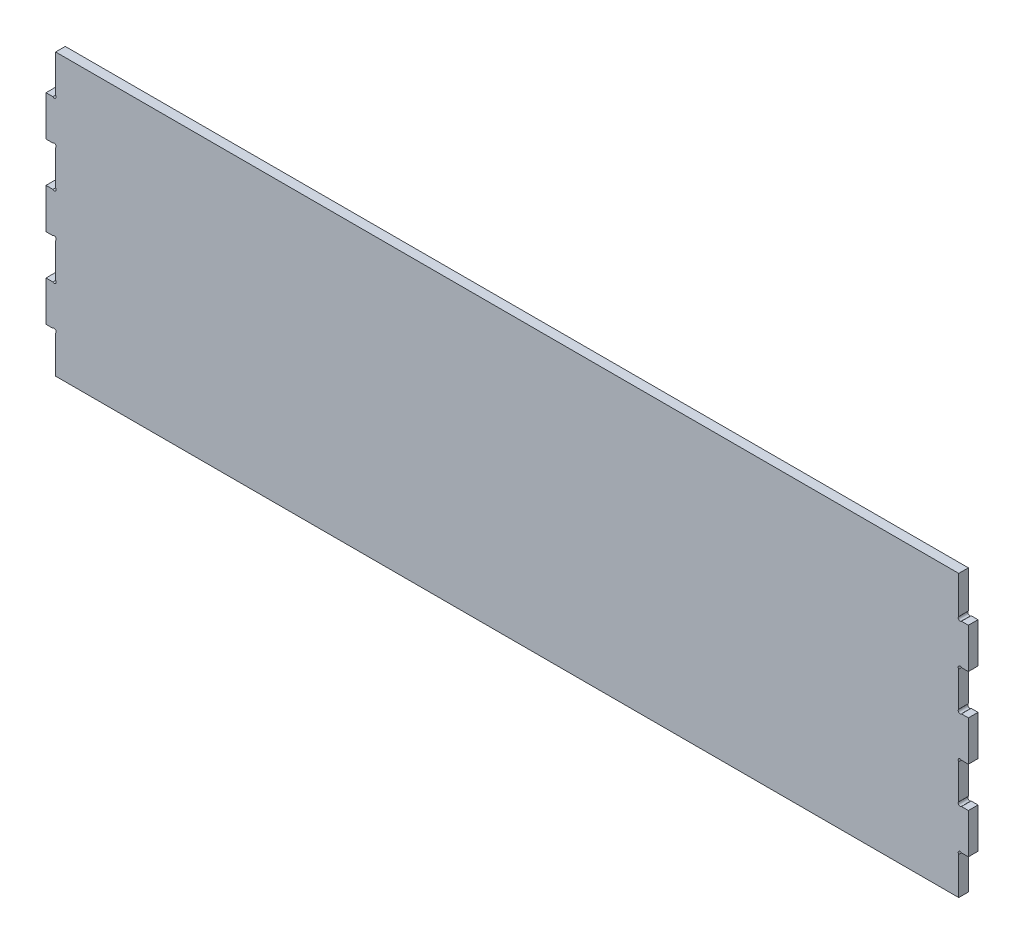
SolidWorks part; units mm, degrees
ref_plane "Front Plane" through (0, 0, 0) normal (0, 0, 1) x (1, 0, 0)
ref_plane "Top Plane" through (0, 0, 0) normal (0, 1, 0) x (1, 0, 0)
ref_plane "Right Plane" through (0, 0, 0) normal (1, 0, 0) x (0, 0, -1)
sketch "Sketch1" plane through (0, 0, 0) normal (0, 0, 1) x (1, 0, 0)
  line L0 (511.8067, 188.9039) -> (511.8067, 142.2993)
  line L1 (-613.9221, 188.9039) -> (511.8067, 188.9039)
  line L2 (-625.9221, -111.0961) -> (-625.9221, -61.0961)
  line L3 (-613.9221, -161.0961) -> (511.8067, -161.0961)
  line L4 (523.8067, 138.3198) -> (523.8067, 88.9039)
  line L5 (512.303, 138.9063) -> (512.303, 88.9039) construction
  line L6 (518.8067, 88.9039) -> (515.202, 88.9039)
  line L7 (511.8067, 85.5109) -> (511.8067, 42.2969)
  line L8 (515.202, 38.9039) -> (518.8067, 38.9039)
  line L9 (523.8067, 38.9039) -> (523.8067, -11.0961)
  line L10 (518.8067, -11.0961) -> (515.202, -11.0961)
  line L11 (511.8067, -14.4891) -> (511.8067, -57.7031)
  line L12 (515.202, -61.0961) -> (518.8067, -61.0961)
  line L13 (523.8067, -61.0961) -> (523.8067, -111.0961)
  line L14 (518.8067, -111.0961) -> (515.202, -111.0961)
  line L15 (511.8067, -114.4891) -> (511.8067, -161.0961)
  line L16 (523.8067, 138.3198) -> (523.8067, 138.9063)
  line L17 (523.8067, 88.9039) -> (518.8067, 88.9039)
  line L18 (518.8067, 38.9039) -> (523.8067, 38.9039)
  line L19 (523.8067, -11.0961) -> (518.8067, -11.0961)
  line L20 (518.8067, -61.0961) -> (523.8067, -61.0961)
  line L21 (523.8067, -111.0961) -> (518.8067, -111.0961)
  line L22 (-625.9221, 88.9039) -> (-625.9221, 138.3198)
  line L23 (523.8067, -98.3448) -> (-625.9221, -98.3448) construction
  line L24 (523.8067, 138.9063) -> (515.202, 138.9063)
  line L25 (512.303, 113.9051) -> (524.4814, 113.9051) construction
  line L26 (512.303, 141.3063) -> (512.303, 140.6015) construction
  line L27 (512.303, 140.6015) -> (513.9987, 140.6015) construction
  line L28 (512.303, 138.9063) -> (514.703, 138.9063) construction
  line L29 (514.703, 138.9063) -> (513.503, 138.9063) construction
  line L30 (513.503, 138.9063) -> (513.503, 140.6015) construction
  line L31 (-625.9221, 138.3198) -> (-625.9221, 138.9063)
  line L32 (512.303, 88.9039) -> (512.303, 38.9039) construction
  line L33 (512.303, 63.9039) -> (525.303, 63.9039) construction
  line L34 (512.303, 38.9039) -> (512.303, -11.0961) construction
  line L35 (512.303, 13.9039) -> (527.9398, 13.9039) construction
  line L36 (512.303, -11.0961) -> (512.303, -61.0961) construction
  line L37 (512.303, -36.0961) -> (527.9398, -36.0961) construction
  line L38 (512.303, -61.0961) -> (512.303, -111.0961) construction
  line L39 (512.303, -86.0961) -> (525.303, -86.0961) construction
  line L40 (-51.0577, -161.0961) -> (-51.0577, 188.9039) construction
  line L41 (-613.9221, -114.4891) -> (-613.9221, -161.0961)
  line L43 (-625.9221, -111.0961) -> (-620.9221, -111.0961)
  line L44 (-620.9221, -111.0961) -> (-617.3174, -111.0961)
  line L45 (-620.9221, -61.0961) -> (-625.9221, -61.0961)
  line L46 (-617.3174, -61.0961) -> (-620.9221, -61.0961)
  line L47 (-613.9221, -14.4891) -> (-613.9221, -57.7031)
  line L48 (-625.9221, -11.0961) -> (-620.9221, -11.0961)
  line L49 (-620.9221, -11.0961) -> (-617.3174, -11.0961)
  line L50 (-620.9221, 38.9039) -> (-625.9221, 38.9039)
  line L51 (-617.3174, 38.9039) -> (-620.9221, 38.9039)
  line L52 (-613.9221, 85.5109) -> (-613.9221, 42.2969)
  line L53 (-620.9221, 88.9039) -> (-617.3174, 88.9039)
  line L54 (-625.9221, 88.9039) -> (-620.9221, 88.9039)
  line L55 (-625.9221, 138.9063) -> (-617.3174, 138.9063)
  line L56 (-619.3744, 138.9063) -> (219.8393, 138.9063) construction
  line L57 (-613.9221, 188.9039) -> (-613.9221, 142.2993)
  line L58 (-625.9221, -11.0961) -> (-625.9221, 38.9039)
  line L62 (-623.4221, 38.9039) -> (236.8492, 38.9039) construction
  line L63 (-619.1198, -61.0961) -> (273.345, -61.0961) construction
  circle A0 centre (512.303, 138.9063) radius 2.4 construction
  arc A1 (511.8067, 142.2993) -> (515.202, 138.9063) centre (513.503, 140.6015) ccw
  arc A2 (511.8067, 85.5109) -> (515.202, 88.9039) centre (513.503, 87.2087) cw
  arc A3 (511.8067, 42.2969) -> (515.202, 38.9039) centre (513.503, 40.599) ccw
  arc A4 (511.8067, -14.4891) -> (515.202, -11.0961) centre (513.503, -12.7913) cw
  arc A5 (511.8067, -57.7031) -> (515.202, -61.0961) centre (513.503, -59.401) ccw
  arc A6 (511.8067, -114.4891) -> (515.202, -111.0961) centre (513.503, -112.7913) cw
  arc A7 (-613.9221, -114.4891) -> (-617.3174, -111.0961) centre (-615.6184, -112.7913) ccw
  arc A8 (-613.9221, -57.7031) -> (-617.3174, -61.0961) centre (-615.6184, -59.401) cw
  arc A9 (-613.9221, -14.4891) -> (-617.3174, -11.0961) centre (-615.6184, -12.7913) ccw
  arc A10 (-613.9221, 42.2969) -> (-617.3174, 38.9039) centre (-615.6184, 40.599) cw
  arc A11 (-613.9221, 85.5109) -> (-617.3174, 88.9039) centre (-615.6184, 87.2087) ccw
  arc A12 (-613.9221, 142.2993) -> (-617.3174, 138.9063) centre (-615.6184, 140.6015) cw
  point P3 (523.8067, 88.9039)
  point P7 (530.298, 138.4807)
  point P8 (523.8067, -11.0961)
  point P10 (523.8067, 38.9039)
  point P12 (523.8067, -111.0961)
  point P14 (523.8067, -61.0961)
  dimension "D11" = 4.8
  dimension "D13" = 4.8
  dimension "D3" = 18
  dimension "D4" = 50
  dimension "D5" = 50
  dimension "D6" = 50
  dimension "D7" = 50
  dimension "D8" = 50
  dimension "D9" = 50
  dimension "D12" = 5
  dimension "D14" = 5
  dimension "D16" = 5
  dimension "D18" = 5
  dimension "D20" = 5
  dimension "D31" = 12
extrude "Boss-Extrude1" add sketch "Sketch1" along normal blind 12
sketch "Sketch2" plane through (0, 0, 0) normal (0, 0, -1) x (-1, 0, 0)
  line L28 (613.9221, 188.9039) -> (-511.8067, 188.9039)
  line L29 (-511.8067, 188.9039) -> (-511.8067, 142.2993)
  line L30 (-515.202, 138.9063) -> (-523.8067, 138.9063)
  line L31 (-523.8067, 138.9063) -> (-523.8067, 88.9039)
  line L32 (-523.8067, 88.9039) -> (-515.202, 88.9039)
  line L33 (-511.8067, 85.5109) -> (-511.8067, 42.2969)
  line L34 (-515.202, 38.9039) -> (-523.8067, 38.9039)
  line L35 (-523.8067, 38.9039) -> (-523.8067, -11.0961)
  line L36 (-523.8067, -11.0961) -> (-515.202, -11.0961)
  line L37 (-511.8067, -14.4891) -> (-511.8067, -57.7031)
  line L38 (-515.202, -61.0961) -> (-523.8067, -61.0961)
  line L39 (-523.8067, -61.0961) -> (-523.8067, -111.0961)
  line L40 (-523.8067, -111.0961) -> (-515.202, -111.0961)
  line L41 (-511.8067, -114.4891) -> (-511.8067, -161.0961)
  line L42 (-511.8067, -161.0961) -> (613.9221, -161.0961)
  line L43 (613.9221, -161.0961) -> (613.9221, -114.4891)
  line L44 (617.3174, -111.0961) -> (625.9221, -111.0961)
  line L45 (625.9221, -111.0961) -> (625.9221, -61.0961)
  line L46 (625.9221, -61.0961) -> (617.3174, -61.0961)
  line L47 (613.9221, -57.7031) -> (613.9221, -14.4891)
  line L48 (617.3174, -11.0961) -> (625.9221, -11.0961)
  line L49 (625.9221, -11.0961) -> (625.9221, 38.9039)
  line L50 (625.9221, 38.9039) -> (617.3174, 38.9039)
  line L51 (613.9221, 42.2969) -> (613.9221, 85.5109)
  line L52 (617.3174, 88.9039) -> (625.9221, 88.9039)
  line L53 (625.9221, 88.9039) -> (625.9221, 138.9063)
  line L54 (625.9221, 138.9063) -> (617.3174, 138.9063)
  line L55 (613.9221, 142.2993) -> (613.9221, 188.9039)
  line L56 (613.9221, 188.9039) -> (-511.8067, 188.9039)
  line L57 (-511.8067, 188.9039) -> (-511.8067, 142.2993)
  line L58 (-515.202, 138.9063) -> (-523.8067, 138.9063)
  line L59 (-523.8067, 138.9063) -> (-523.8067, 88.9039)
  line L60 (-523.8067, 88.9039) -> (-515.202, 88.9039)
  line L61 (-511.8067, 85.5109) -> (-511.8067, 42.2969)
  line L62 (-515.202, 38.9039) -> (-523.8067, 38.9039)
  line L63 (-523.8067, 38.9039) -> (-523.8067, -11.0961)
  line L64 (-523.8067, -11.0961) -> (-515.202, -11.0961)
  line L65 (-511.8067, -14.4891) -> (-511.8067, -57.7031)
  line L66 (-515.202, -61.0961) -> (-523.8067, -61.0961)
  line L67 (-523.8067, -61.0961) -> (-523.8067, -111.0961)
  line L68 (-523.8067, -111.0961) -> (-515.202, -111.0961)
  line L69 (-511.8067, -114.4891) -> (-511.8067, -161.0961)
  line L70 (-511.8067, -161.0961) -> (613.9221, -161.0961)
  line L71 (613.9221, -161.0961) -> (613.9221, -114.4891)
  line L72 (617.3174, -111.0961) -> (625.9221, -111.0961)
  line L73 (625.9221, -111.0961) -> (625.9221, -61.0961)
  line L74 (625.9221, -61.0961) -> (617.3174, -61.0961)
  line L75 (613.9221, -57.7031) -> (613.9221, -14.4891)
  line L76 (617.3174, -11.0961) -> (625.9221, -11.0961)
  line L77 (625.9221, -11.0961) -> (625.9221, 38.9039)
  line L78 (625.9221, 38.9039) -> (617.3174, 38.9039)
  line L79 (613.9221, 42.2969) -> (613.9221, 85.5109)
  line L80 (617.3174, 88.9039) -> (625.9221, 88.9039)
  line L81 (625.9221, 88.9039) -> (625.9221, 138.9063)
  line L82 (625.9221, 138.9063) -> (617.3174, 138.9063)
  line L83 (613.9221, 142.2993) -> (613.9221, 188.9039)
  arc A12 (-515.202, 138.9063) -> (-511.8067, 142.2993) centre (-513.503, 140.6015) ccw
  arc A13 (-511.8067, 85.5109) -> (-515.202, 88.9039) centre (-513.503, 87.2087) ccw
  arc A14 (-515.202, 38.9039) -> (-511.8067, 42.2969) centre (-513.503, 40.599) ccw
  arc A15 (-511.8067, -14.4891) -> (-515.202, -11.0961) centre (-513.503, -12.7913) ccw
  arc A16 (-515.202, -61.0961) -> (-511.8067, -57.7031) centre (-513.503, -59.401) ccw
  arc A17 (-511.8067, -114.4891) -> (-515.202, -111.0961) centre (-513.503, -112.7913) ccw
  arc A18 (617.3174, -111.0961) -> (613.9221, -114.4891) centre (615.6184, -112.7913) ccw
  arc A19 (613.9221, -57.7031) -> (617.3174, -61.0961) centre (615.6184, -59.401) ccw
  arc A20 (617.3174, -11.0961) -> (613.9221, -14.4891) centre (615.6184, -12.7913) ccw
  arc A21 (613.9221, 42.2969) -> (617.3174, 38.9039) centre (615.6184, 40.599) ccw
  arc A22 (617.3174, 88.9039) -> (613.9221, 85.5109) centre (615.6184, 87.2087) ccw
  arc A23 (613.9221, 142.2993) -> (617.3174, 138.9063) centre (615.6184, 140.6015) ccw
  arc A24 (-515.202, 138.9063) -> (-511.8067, 142.2993) centre (-513.503, 140.6015) ccw
  arc A25 (-511.8067, 85.5109) -> (-515.202, 88.9039) centre (-513.503, 87.2087) ccw
  arc A26 (-515.202, 38.9039) -> (-511.8067, 42.2969) centre (-513.503, 40.599) ccw
  arc A27 (-511.8067, -14.4891) -> (-515.202, -11.0961) centre (-513.503, -12.7913) ccw
  arc A28 (-515.202, -61.0961) -> (-511.8067, -57.7031) centre (-513.503, -59.401) ccw
  arc A29 (-511.8067, -114.4891) -> (-515.202, -111.0961) centre (-513.503, -112.7913) ccw
  arc A30 (617.3174, -111.0961) -> (613.9221, -114.4891) centre (615.6184, -112.7913) ccw
  arc A31 (613.9221, -57.7031) -> (617.3174, -61.0961) centre (615.6184, -59.401) ccw
  arc A32 (617.3174, -11.0961) -> (613.9221, -14.4891) centre (615.6184, -12.7913) ccw
  arc A33 (613.9221, 42.2969) -> (617.3174, 38.9039) centre (615.6184, 40.599) ccw
  arc A34 (617.3174, 88.9039) -> (613.9221, 85.5109) centre (615.6184, 87.2087) ccw
  arc A35 (613.9221, 142.2993) -> (617.3174, 138.9063) centre (615.6184, 140.6015) ccw
  dimension "D1" = 0
